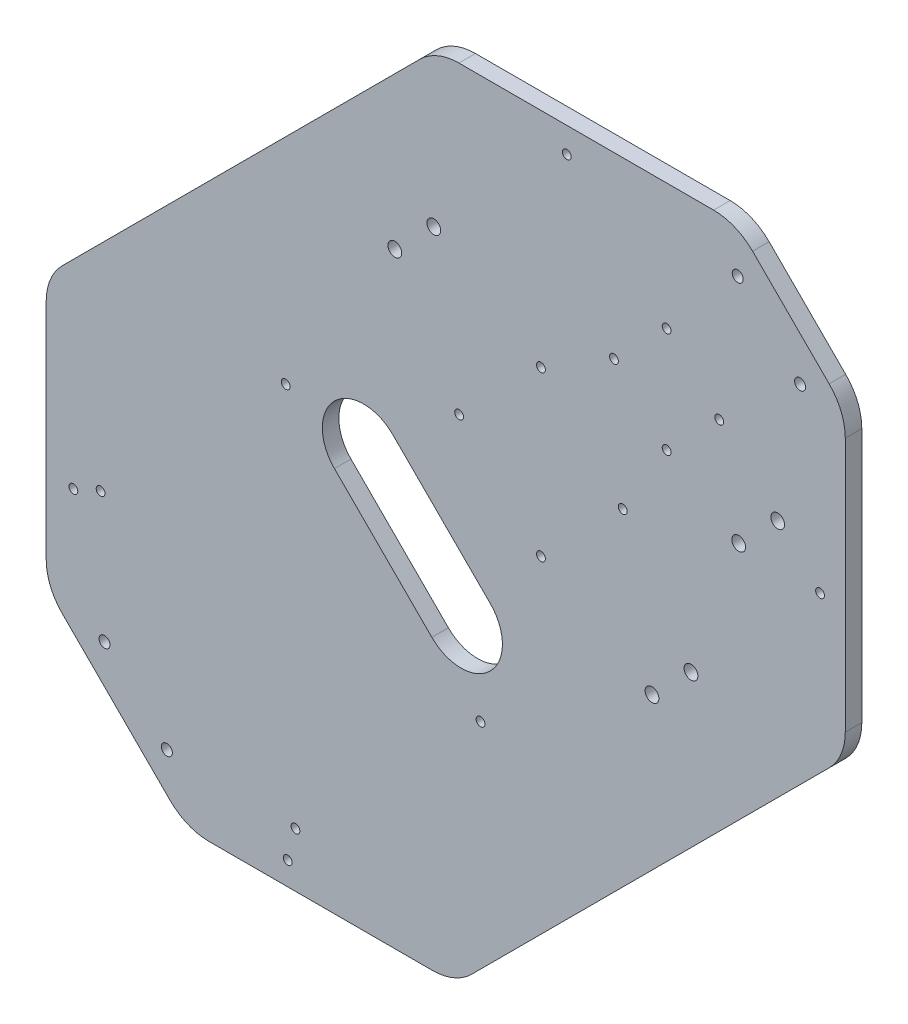
SolidWorks part; units mm, degrees
ref_plane "Front Plane" through (0, 0, 0) normal (0, 0, 1) x (1, 0, 0)
ref_plane "Top Plane" through (0, 0, 0) normal (0, 1, 0) x (1, 0, 0)
ref_plane "Right Plane" through (0, 0, 0) normal (1, 0, 0) x (0, 0, -1)
sketch "Sketch1" plane through (0, 0, 0) normal (0, 0, 1) x (1, 0, 0)
  line L0 (-209.5706, 21.043) -> (-79.7788, 150.8349)
  line L1 (-220.4285, 161.6928) -> (79.5715, 161.6928) construction
  line L2 (-220.4285, 161.6928) -> (-220.4285, -138.3072) construction
  line L3 (-220.4285, -138.3072) -> (79.5715, -138.3072) construction
  line L4 (79.5715, 161.6928) -> (79.5715, -138.3072) construction
  line L5 (40.9319, 150.8349) -> (68.7137, 123.0531)
  line L6 (-209.5706, -88.3539) -> (-170.4751, -127.4494)
  line L7 (68.7137, 2.3425) -> (-61.0782, -127.4494)
  line L8 (79.5715, 161.6928) -> (-220.4285, -138.3072) construction
  line L9 (-194.2655, -89.5169) -> (-171.6381, -112.1443) construction
  line L10 (-65.5721, 46.2476) -> (-35.8736, 16.5491) construction
  line L11 (-215.4285, 6.9009) -> (-215.4285, -74.2118)
  line L12 (-156.333, -133.3072) -> (-75.2203, -133.3072)
  line L13 (74.5715, 16.4846) -> (74.5715, 108.911)
  line L14 (-65.6366, 156.6928) -> (26.7898, 156.6928)
  line L15 (-205.5664, -47.1033) -> (-127.7846, -124.8851) construction
  line L16 (-128.5046, 24.3273) -> (-57.7939, -46.3834) construction
  line L17 (-128.5046, 24.3273) -> (-195.6797, -42.8478) construction
  line L18 (-195.6797, -42.8478) -> (-124.9691, -113.5585) construction
  line L19 (-57.7939, -46.3834) -> (-124.9691, -113.5585) construction
  line L20 (-65.5721, 46.2476) -> (-35.8736, 75.9461) construction
  line L21 (-35.8736, 16.5491) -> (-6.1751, 46.2476) construction
  line L22 (-35.8736, 75.9461) -> (-6.1751, 46.2476) construction
  line L23 (-100.2203, 17.2562) -> (-64.865, -18.0991) construction
  line L24 (-89.6137, 27.8629) -> (-54.2584, -7.4925)
  line L25 (-110.8269, 6.6496) -> (-75.4716, -28.7057)
  line L26 (-9.3571, 91.856) -> (9.7348, 72.7641) construction
  line L27 (-9.3571, 91.856) -> (9.7348, 110.9479) construction
  line L28 (9.7348, 72.7641) -> (28.8267, 91.856) construction
  line L29 (9.7348, 110.9479) -> (28.8267, 91.856) construction
  line L30 (35.5471, 140.2957) -> (58.1745, 117.6683) construction
  line L31 (50.0399, 70.6428) -> (35.8977, 56.5007) construction
  line L32 (18.5736, 7.3568) -> (4.4315, -6.7854) construction
  line L33 (-74.7645, 100.6948) -> (-88.9066, 86.5527) construction
  line L36 (-26.4945, 147.5506) -> (65.4294, 55.6267) construction
  circle A0 centre (-194.2655, -89.5169) radius 2
  circle A1 centre (-171.6381, -112.1443) radius 2
  arc A2 (-89.6137, 27.8629) -> (-110.8269, 6.6496) centre (-100.2203, 17.2562) ccw
  arc A3 (-75.4716, -28.7057) -> (-54.2584, -7.4925) centre (-64.865, -18.0991) ccw
  arc A4 (-215.4285, 6.9009) -> (-209.5706, 21.043) centre (-195.4285, 6.9009) cw
  arc A5 (-215.4285, -74.2118) -> (-209.5706, -88.3539) centre (-195.4285, -74.2118) ccw
  arc A6 (-156.333, -133.3072) -> (-170.4751, -127.4494) centre (-156.333, -113.3072) cw
  arc A7 (-75.2203, -133.3072) -> (-61.0782, -127.4494) centre (-75.2203, -113.3072) ccw
  arc A8 (74.5715, 16.4846) -> (68.7137, 2.3425) centre (54.5715, 16.4846) cw
  arc A9 (74.5715, 108.911) -> (68.7137, 123.0531) centre (54.5715, 108.911) ccw
  arc A10 (26.7898, 156.6928) -> (40.9319, 150.8349) centre (26.7898, 136.6928) cw
  arc A11 (-65.6366, 156.6928) -> (-79.7788, 150.8349) centre (-65.6366, 136.6928) ccw
  circle A12 centre (-195.6797, -42.8478) radius 1.6
  circle A13 centre (-124.9691, -113.5585) radius 1.6
  circle A14 centre (-57.7939, -46.3834) radius 1.6
  circle A15 centre (-128.5046, 24.3273) radius 1.6
  circle A16 centre (-205.5664, -47.1033) radius 1.6
  circle A17 centre (-127.7846, -124.8851) radius 1.6
  circle A18 centre (-65.5721, 46.2476) radius 1.6
  circle A19 centre (-35.8736, 16.5491) radius 1.6
  circle A20 centre (-6.1751, 46.2476) radius 1.6
  circle A21 centre (-35.8736, 75.9461) radius 1.6
  circle A22 centre (-9.3571, 91.856) radius 1.6
  circle A23 centre (9.7348, 72.7641) radius 1.6
  circle A24 centre (28.8267, 91.856) radius 1.6
  circle A25 centre (9.7348, 110.9479) radius 1.6
  circle A26 centre (35.5471, 140.2957) radius 2
  circle A27 centre (58.1745, 117.6683) radius 2
  circle A28 centre (50.0399, 70.6428) radius 2.5
  circle A29 centre (35.8977, 56.5007) radius 2.5
  circle A30 centre (18.5736, 7.3568) radius 2.5
  circle A31 centre (4.4315, -6.7854) radius 2.5
  circle A32 centre (-74.7645, 100.6948) radius 2.5
  circle A33 centre (-88.9066, 86.5527) radius 2.5
  circle A34 centre (-26.4945, 147.5506) radius 1.6
  circle A35 centre (65.4294, 55.6267) radius 1.6
  point P6 (-93.1492, -11.028)
  point P8 (-182.9518, -100.8306)
  point P10 (-50.7228, 31.3984)
  point P51 (-82.5426, -0.4214)
  point P61 (46.8608, 128.982)
  point P71 (19.2807, 101.402)
  point P76 (0, 0)
  point P81 (0, 0)
  point P82 (0, 0)
  point P95 (19.4675, 101.5887)
  dimension "D6" = 4
  dimension "D15" = 20
  dimension "D16" = 20
  dimension "D17" = 20
  dimension "D18" = 20
  dimension "D19" = 20
  dimension "D20" = 20
  dimension "D21" = 20
  dimension "D22" = 20
  dimension "D25" = 3.2
  dimension "D28" = 3.2
  dimension "D45" = 20
  dimension "D31" = 15
  dimension "D33" = 3.2
  dimension "D38" = 4
  dimension "D40" = 5
  dimension "D41" = 20
  dimension "D1" = 300
  dimension "D2" = 300
  dimension "D3" = 210
  dimension "D4" = 32
  dimension "D5" = 20
  dimension "D7" = 42
  dimension "D8" = 43
  dimension "D9" = 35
  dimension "D10" = 5
  dimension "D11" = 5
  dimension "D12" = 5
  dimension "D13" = 5
  dimension "D14" = 10
  dimension "D23" = 95
  dimension "D24" = 100
  dimension "D26" = 85
  dimension "D27" = 110
  dimension "D29" = 75
  dimension "D30" = 50
  dimension "D32" = 195
  dimension "D34" = 30
  dimension "D35" = 27
  dimension "D36" = 30
  dimension "D37" = 32
  dimension "D39" = 46.26
  dimension "D42" = 30
  dimension "D43" = 30
  dimension "D44" = 45
  dimension "D46" = 20
  dimension "D47" = 45
  dimension "D48" = 130
  dimension "D49" = 85
  dimension "D50" = 30
extrude "Boss-Extrude1" add sketch "Sketch1" along normal blind 6
